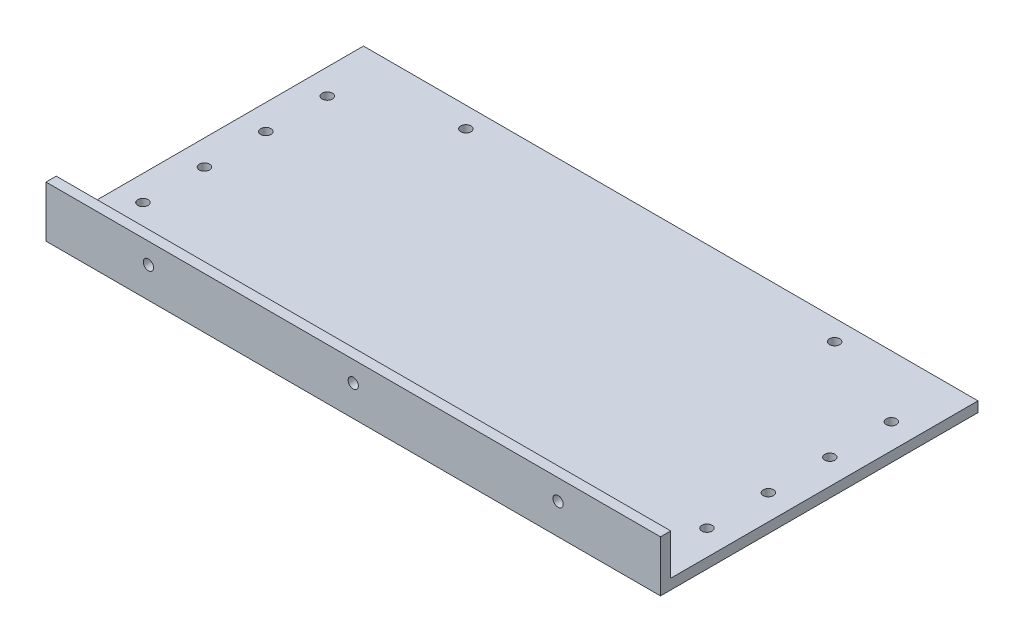
SolidWorks part; units mm, degrees
material "6061-T6 (SS)"
ref_plane "Front Plane" through (0, 0, 0) normal (0, 0, 1) x (1, 0, 0)
ref_plane "Top Plane" through (0, 0, 0) normal (0, 1, 0) x (1, 0, 0)
ref_plane "Right Plane" through (0, 0, 0) normal (1, 0, 0) x (0, 0, -1)
sketch "Sketch1" plane through (0, 0, 0) normal (0, 1, 0) x (1, 0, 0)
  line L1 (-190.5, -95.25) -> (190.5, -95.25)
  line L2 (-190.5, -95.25) -> (-190.5, 95.25)
  line L3 (-190.5, 95.25) -> (190.5, 95.25)
  line L4 (190.5, -95.25) -> (190.5, 95.25)
  point P4 (0, 95.25)
  point P6 (-190.5, 0)
  dimension "D1" = 381
  dimension "D2" = 190.5
extrude "Boss-Extrude1" add sketch "Sketch1" along normal blind 6.35
sketch "Sketch2" plane through (0, 0, 95.25) normal (0, 0, 1) x (1, 0, 0)
  line L1 (-190.5, 0) -> (190.5, 0)
  line L2 (-190.5, 0) -> (-190.5, 31.75)
  line L3 (-190.5, 31.75) -> (190.5, 31.75)
  line L4 (190.5, 0) -> (190.5, 31.75)
  dimension "D1" = 31.75
extrude "Boss-Extrude2" add sketch "Sketch2" along normal blind 6.35
sketch "Sketch3" plane through (0, 0, 101.6) normal (0, 0, 1) x (1, 0, 0)
  line L0 (0, 0) -> (0, 31.75) construction
  line L1 (-190.5, 0) -> (190.5, 0) construction
  line L2 (190.5, 31.75) -> (-190.5, 31.75) construction
  circle A0 centre (0, 19.05) radius 3.175
  circle A1 centre (-127, 19.05) radius 3.175
  circle A2 centre (127, 19.05) radius 3.175
  dimension "D1" = 6.35
  dimension "D2" = 12.7
  dimension "D3" = 127
  dimension "D4" = 127
extrude "Cut-Extrude1" cut sketch "Sketch3" against normal up to surface (6.35 mm away) up to face at (0, 19.05, 95.25)
sketch "Sketch4" plane through (0, 0, 0) normal (0, -1, 0) x (1, 0, 0)
  line L0 (-190.5, 101.6) -> (190.5, 101.6) construction
  line L2 (190.5, -95.25) -> (-190.5, -95.25) construction
  circle A0 centre (0, 82.55) radius 3.175
  circle A1 centre (-114.3, 82.55) radius 3.175
  circle A2 centre (114.3, 82.55) radius 3.175
  circle A3 centre (-114.3, -82.55) radius 3.175
  circle A5 centre (114.3, -82.55) radius 3.175
  dimension "D2" = 6.35
  dimension "D3" = 114.3
  dimension "D5" = 12.7
  dimension "D1" = 19.05
  dimension "D4" = 114.3
extrude "Cut-Extrude2" cut sketch "Sketch4" against normal up to surface (6.35 mm away) up to face at (0, 6.35, 0)
sketch "Sketch5" plane through (0, 0, 0) normal (0, -1, 0) x (1, 0, 0)
  line L0 (190.5, 101.6) -> (190.5, -95.25) construction
  line L1 (-190.5, 95.25) -> (190.5, 95.25) construction
  line L2 (-190.5, 95.25) -> (190.5, 95.25) construction
  line L3 (0, 0) -> (0, 229.4543) construction
  circle A2 centre (174.8536, 57.15) radius 3.175
  circle A8 centre (174.8536, 19.05) radius 3.175
  circle A9 centre (174.8536, -19.05) radius 3.175
  circle A10 centre (174.8536, -57.15) radius 3.175
  circle A11 centre (-174.8536, -57.15) radius 3.175
  circle A12 centre (-174.8536, -19.05) radius 3.175
  circle A13 centre (-174.8536, 19.05) radius 3.175
  circle A14 centre (-174.8536, 57.15) radius 3.175
  dimension "D1" = 6.35
  dimension "D2" = 15.6464
  dimension "D3" = 38.1
  dimension "D5" = 38.1
  dimension "D4" = 4
extrude "Cut-Extrude3" cut sketch "Sketch5" against normal up to surface (6.35 mm away) up to face at (114.3, 6.35, -85.725)
